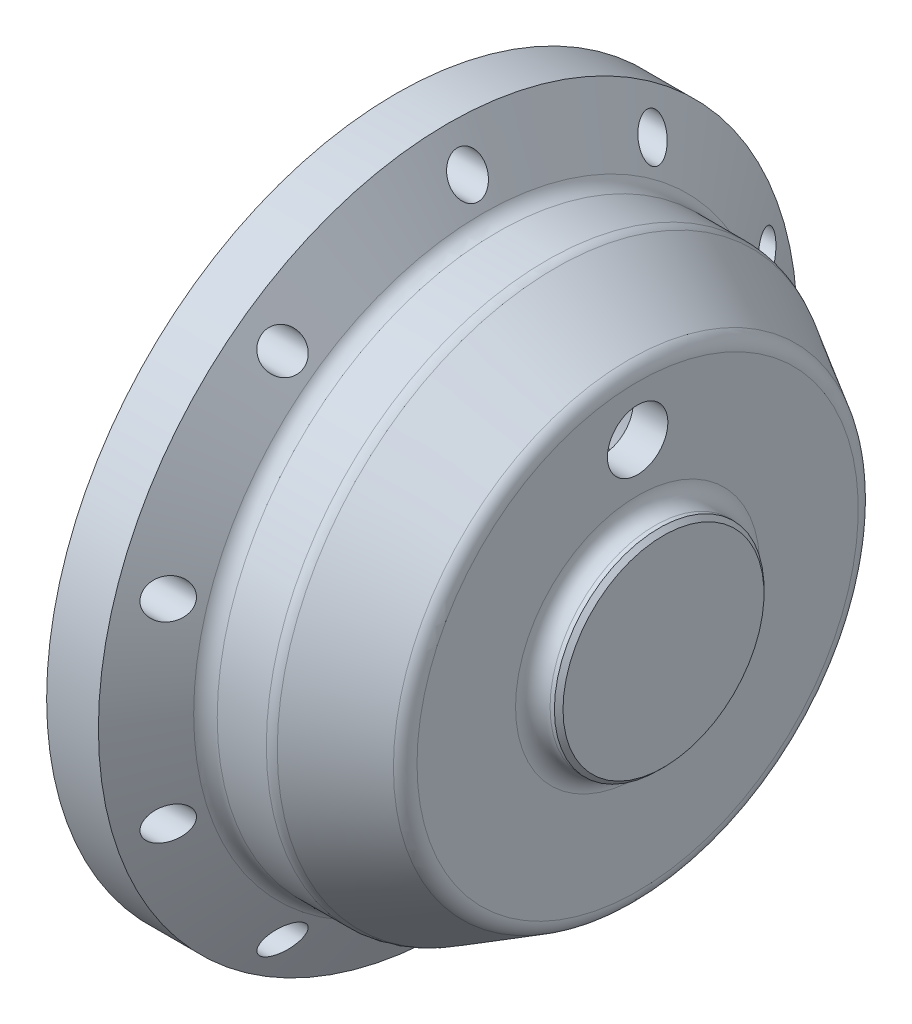
SolidWorks part; units mm, degrees
material "6061-T6 (SS)"
ref_plane "Front Plane" through (0, 0, 0) normal (0, 0, 1) x (1, 0, 0)
ref_plane "Top Plane" through (0, 0, 0) normal (0, 1, 0) x (1, 0, 0)
ref_plane "Right Plane" through (0, 0, 0) normal (1, 0, 0) x (0, 0, -1)
ref_axis "Axis1" through (-90.2206, 0, 0) along (1, 0, 0)
sketch "Sketch1" plane through (0, 0, 0) normal (0, 0, 1) x (1, 0, 0)
  line L0 (0, 40.5) -> (0, 30.475)
  line L1 (0, 30.475) -> (-1, 30.475)
  line L2 (-1, 30.475) -> (-1, 25.475)
  line L3 (-1, 25.475) -> (22, 25.475)
  line L5 (10, 7.5) -> (26.5, 7.5)
  line L6 (28, 14.15) -> (28, 25.5718)
  line L7 (17.4641, 32.5) -> (11.7735, 32.5)
  line L8 (-90.2206, 0) -> (87.7594, 0) construction
  line L10 (7.5, 12.15) -> (23.5, 12.15)
  line L11 (24, 12.65) -> (24, 23.475)
  line L16 (27, 7) -> (27, 0)
  line L17 (27, 0) -> (31, 0)
  line L19 (10, 7.5) -> (10, 11.15)
  line L22 (10.0415, 33.5) -> (6, 40.5)
  line L23 (6, 40.5) -> (0, 40.5)
  line L24 (10, 11.15) -> (7.5, 11.15)
  line L25 (7.5, 11.15) -> (7.5, 12.15)
  line L26 (30, 12.15) -> (30.5, 12.15)
  line L27 (31, 11.65) -> (31, 0)
  line L28 (27, 27.3038) -> (18.4641, 32.2321)
  line L29 (30.5, 12.15) -> (31, 11.65)
  arc A0 (23.5, 12.15) -> (24, 12.65) centre (23.5, 12.65) ccw
  arc A1 (22, 25.475) -> (24, 23.475) centre (22, 23.475) cw
  arc A2 (26.5, 7.5) -> (27, 7) centre (26.5, 7) cw
  arc A3 (10.0415, 33.5) -> (11.7735, 32.5) centre (11.7735, 34.5) ccw
  arc A4 (30, 12.15) -> (28, 14.15) centre (30, 14.15) cw
  arc A5 (27, 27.3038) -> (28, 25.5718) centre (26, 25.5718) cw
  arc A6 (18.4641, 32.2321) -> (17.4641, 32.5) centre (17.4641, 30.5) ccw
  point P9 (28, 32.5)
  point P27 (31, 12.15)
  point P38 (18, 32.5)
  dimension "D12" = 0.5
  dimension "D17" = 2
  dimension "D14" = 2
  dimension "D22" = 2
  dimension "D23" = 0.5
  dimension "D1" = 60.95
  dimension "D2" = 15
  dimension "D3" = 65
  dimension "D4" = 5
  dimension "D5" = 1
  dimension "D6" = 4
  dimension "D7" = 4
  dimension "D8" = 25
  dimension "D9" = 2.5
  dimension "D10" = 11.15
  dimension "D11" = 1
  dimension "D13" = 30
  dimension "D15" = 8
  dimension "D16" = 60
  dimension "D18" = 10
  dimension "D20" = 27
  dimension "D21" = 6
revolve "Revolve1" add sketch "Sketch1" angle 360 about axis through (-90.2206, 0, 0) along (1, 0, 0)
hole_wizard "Tapped Hole for M4x0.7 Helicoil1" positions "Sketch3" profile "Sketch2" tap size "M4x0.7" standard "Helicoil® Metric"
sketch "Sketch3" plane through (0, 0, 0) normal (1, 0, 0) x (0, 0, -1)
  point P1 (0, 36.5)
  dimension "D1" = 36.5
sketch "Sketch2" plane through (0, 36.5, 0) normal (0, 1, 0) x (0, 0, 1)
  line L0 (0, 0) -> (0, 13.5618)
  line L1 (0, 13.5618) -> (2.1, 12.3)
  line L2 (2.1, 12.3) -> (2.1, 0)
  line L5 (2.1, 0) -> (0, 0)
  line L10 (0, 13.5618) -> (-2.1, 12.3) construction
  line L11 (0, -6.35) -> (0, 107.95) construction
  dimension "Tap Drill Dia." = 4.2
  dimension "Tap Drill Depth" = 12.3
  dimension "Drill Angle" = 118
cosmetic thread "Hole Thread1" parameters "D1"=6, "D2"=5.007
pattern_circular "CirPattern1" count 10 over 360 about axis through (0, 0, 0) along (1, 0, 0) of "Tapped Hole for M4x0.7 Helicoil1"
cosmetic thread "Hole Thread2" parameters "D1"=6, "D2"=5.007
cosmetic thread "Hole Thread3" parameters "D1"=6, "D2"=5.007
cosmetic thread "Hole Thread4" parameters "D1"=6, "D2"=5.007
cosmetic thread "Hole Thread5" parameters "D1"=6, "D2"=5.007
cosmetic thread "Hole Thread6" parameters "D1"=6, "D2"=5.007
cosmetic thread "Hole Thread7" parameters "D1"=6, "D2"=5.007
cosmetic thread "Hole Thread8" parameters "D1"=6, "D2"=5.007
cosmetic thread "Hole Thread9" parameters "D1"=6, "D2"=5.007
cosmetic thread "Hole Thread10" parameters "D1"=6, "D2"=5.007
hole_wizard "Ø7.0 (7) Diameter Hole1" positions "Sketch4" profile "Sketch5" hole size "Ø7.0" standard "ISO" end condition through all
sketch "Sketch4" plane through (0, 0, 0) normal (1, 0, 0) x (0, 0, -1)
  line L0 (0, 19.75) -> (0, 0)
  point P0 (0, 19.75)
  dimension "D1" = 19.75
sketch "Sketch5" plane through (0, 19.75, 0) normal (0, 1, 0) x (0, 0, 1)
  line L0 (0, 0) -> (0, 31)
  line L1 (0, 31) -> (3.5, 31)
  line L2 (3.5, 31) -> (3.5, 0)
  line L5 (3.5, 0) -> (0, 0)
  line L11 (0, -6.35) -> (0, 107.95) construction
  dimension "Thru Hole Dia." = 7
  dimension "Thru Hole Depth" = 31
